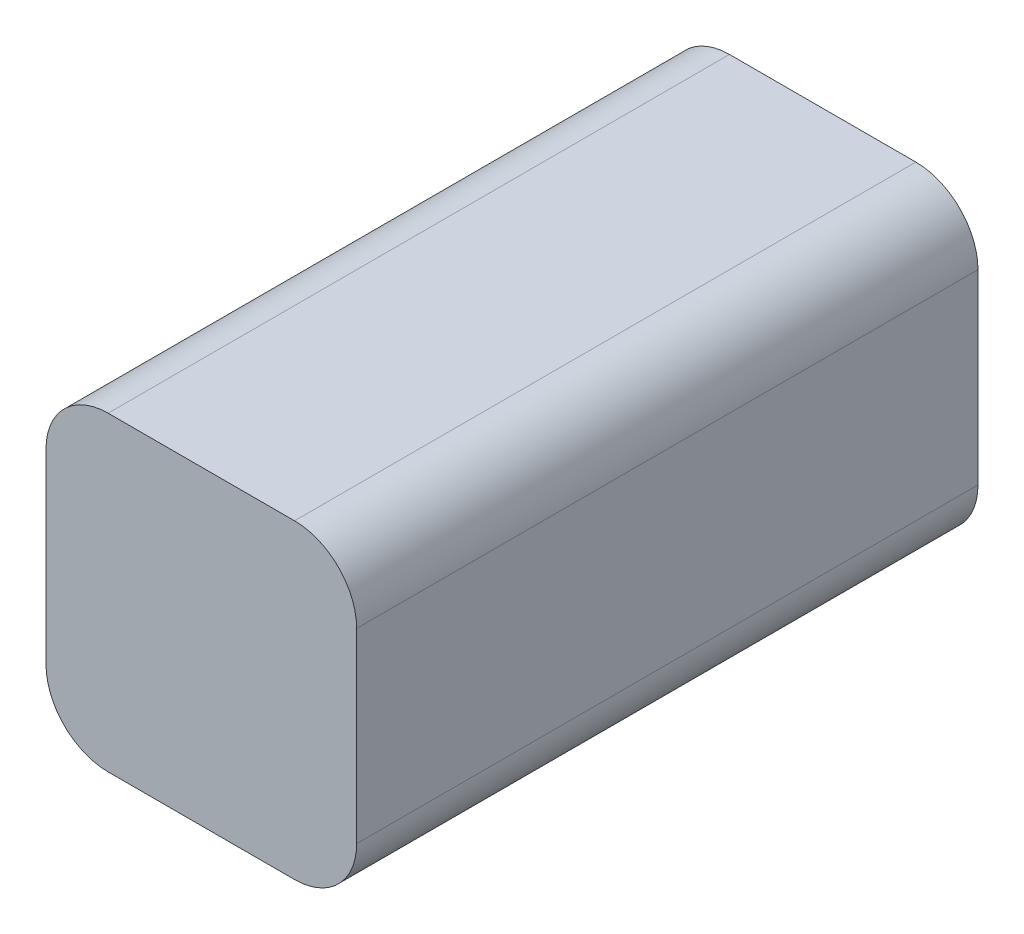
SolidWorks part; units mm, degrees
ref_plane "Ön Düzlem" through (0, 0, 0) normal (0, 0, 1) x (1, 0, 0)
ref_plane "Üst Düzlem" through (0, 0, 0) normal (0, 1, 0) x (1, 0, 0)
ref_plane "Sağ Düzlem" through (0, 0, 0) normal (1, 0, 0) x (0, 0, -1)
sketch "Çizim1" plane through (0, 0, 0) normal (0, 0, 1) x (1, 0, 0)
  line L1 (-7.5, 12.5) -> (7.5, 12.5)
  line L2 (-12.5, 7.5) -> (-12.5, -7.5)
  line L3 (-7.5, -12.5) -> (7.5, -12.5)
  line L4 (12.5, 7.5) -> (12.5, -7.5)
  line L5 (-12.5, 12.5) -> (12.5, -12.5) construction
  line L6 (-12.5, -12.5) -> (12.5, 12.5) construction
  arc A0 (-12.5, -7.5) -> (-7.5, -12.5) centre (-7.5, -7.5) ccw
  arc A1 (7.5, -12.5) -> (12.5, -7.5) centre (7.5, -7.5) ccw
  arc A2 (7.5, 12.5) -> (12.5, 7.5) centre (7.5, 7.5) cw
  arc A3 (-7.5, 12.5) -> (-12.5, 7.5) centre (-7.5, 7.5) ccw
  point P0 (0, 0)
  dimension "D1" = 5
extrude "Yükseklik-Ekstrüzyon1" add sketch "Çizim1" along normal blind 50
sketch "Çizim2" plane through (0, 0, 0) normal (0, 0, 1) x (1, 0, 0)
  line L1 (1.75, 3.75) -> (-1.75, 3.75)
  line L2 (3.75, 1.75) -> (3.75, -1.75)
  line L3 (1.75, -3.75) -> (-1.75, -3.75)
  line L4 (-3.75, 1.75) -> (-3.75, -1.75)
  line L5 (3.75, 3.75) -> (-3.75, -3.75) construction
  line L6 (3.75, -3.75) -> (-3.75, 3.75) construction
  arc A0 (3.75, -1.75) -> (1.75, -3.75) centre (1.75, -1.75) cw
  arc A1 (-1.75, -3.75) -> (-3.75, -1.75) centre (-1.75, -1.75) cw
  arc A2 (-1.75, 3.75) -> (-3.75, 1.75) centre (-1.75, 1.75) ccw
  arc A3 (1.75, 3.75) -> (3.75, 1.75) centre (1.75, 1.75) cw
  point P0 (0, 0)
  dimension "D1" = 2
extrude "Yükseklik-Ekstrüzyon2" add sketch "Çizim2" against normal blind 7.5
